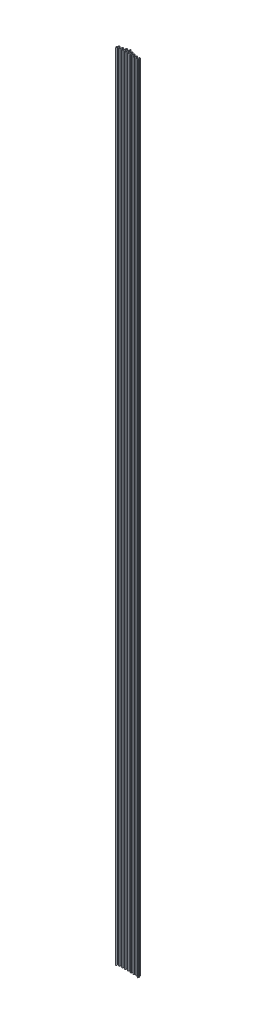
SolidWorks part; units mm, degrees
material "6463-T6"
ref_plane "Front Plane" through (0, 0, 0) normal (0, 0, 1) x (1, 0, 0)
ref_plane "Top Plane" through (0, 0, 0) normal (0, 1, 0) x (1, 0, 0)
ref_plane "Right Plane" through (0, 0, 0) normal (1, 0, 0) x (0, 0, -1)
sketch "Sketch1" plane through (0, 0, 0) normal (0, 1, 0) x (1, 0, 0)
  line L0 (0, 0) -> (101.6, 0) construction
  line L1 (0, 0) -> (0, 19.05) construction
  line L2 (0, 19.05) -> (101.6, 19.05) construction
  line L3 (101.6, 19.05) -> (101.6, 0) construction
  line L4 (0, 6.35) -> (101.6, 6.35) construction
  line L5 (0, 8.89) -> (101.6, 8.89) construction
  line L6 (0, 12.7) -> (101.6, 12.7) construction
  line L7 (0, 16.51) -> (101.6, 16.51) construction
  line L8 (6.35, 0) -> (6.35, 19.05) construction
  line L9 (12.7, 0) -> (12.7, 19.05) construction
  line L10 (19.05, 0) -> (19.05, 19.05) construction
  line L11 (25.4, 0) -> (25.4, 19.05) construction
  line L12 (31.75, 0) -> (31.75, 19.05) construction
  line L13 (38.1, 0) -> (38.1, 19.05) construction
  line L14 (44.45, 0) -> (44.45, 19.05) construction
  line L15 (50.8, 0) -> (50.8, 19.05) construction
  line L16 (57.15, 0) -> (57.15, 19.05) construction
  line L17 (63.5, 0) -> (63.5, 19.05) construction
  line L18 (69.85, 0) -> (69.85, 19.05) construction
  line L19 (76.2, 0) -> (76.2, 19.05) construction
  line L20 (82.55, 0) -> (82.55, 19.05) construction
  line L21 (88.9, 0) -> (88.9, 19.05) construction
  line L22 (95.25, 0) -> (95.25, 19.05) construction
  line L23 (0, 1.6002) -> (101.6, 1.6002) construction
  line L24 (0, 3.2004) -> (101.6, 3.2004) construction
  line L25 (1.4865, 1.0077) -> (3.9905, 7.2904)
  line L26 (11.2135, 1.0077) -> (8.7095, 7.2904)
  line L27 (16.6048, 9.5774) -> (14.2405, 1.1671)
  line L28 (23.8595, 1.1671) -> (21.4952, 9.5774)
  line L29 (26.9714, 1.2981) -> (29.2557, 13.1795)
  line L30 (36.5286, 1.2981) -> (34.2443, 13.1795)
  line L31 (39.6836, 1.3701) -> (41.9364, 16.8752)
  line L32 (49.2164, 1.3701) -> (46.9636, 16.8752)
  line L33 (52.3714, 1.2981) -> (54.6557, 13.1795)
  line L34 (61.9286, 1.2981) -> (59.6443, 13.1795)
  line L35 (65.0405, 1.1671) -> (67.4048, 9.5774)
  line L36 (74.6595, 1.1671) -> (72.2952, 9.5774)
  line L37 (77.6865, 1.0077) -> (80.1905, 7.2904)
  line L38 (87.4135, 1.0077) -> (84.9095, 7.2904)
  line L39 (90.3865, 1.0077) -> (92.8905, 7.2904)
  line L40 (100.1135, 1.0077) -> (97.6095, 7.2904)
  line L59 (2.9022, 0.4435) -> (5.4062, 6.7262)
  line L60 (9.7978, 0.4435) -> (7.2938, 6.7262)
  line L61 (18.0719, 9.165) -> (15.7076, 0.7547)
  line L62 (22.3924, 0.7547) -> (20.0281, 9.165)
  line L63 (28.468, 1.0104) -> (30.7523, 12.8918)
  line L64 (35.032, 1.0104) -> (32.7477, 12.8918)
  line L65 (41.1917, 1.151) -> (43.4446, 16.6561)
  line L66 (47.7083, 1.151) -> (45.4554, 16.6561)
  line L67 (53.868, 1.0104) -> (56.1523, 12.8918)
  line L68 (60.432, 1.0104) -> (58.1477, 12.8918)
  line L69 (66.5076, 0.7547) -> (68.8719, 9.165)
  line L70 (73.1924, 0.7547) -> (70.8281, 9.165)
  line L71 (79.1022, 0.4435) -> (81.6062, 6.7262)
  line L72 (85.9978, 0.4435) -> (83.4938, 6.7262)
  line L73 (91.8022, 0.4435) -> (94.3062, 6.7262)
  line L74 (98.6978, 0.4435) -> (96.1938, 6.7262)
  line L75 (101.6, 0) -> (101.6, -1.524)
  line L76 (0, 0) -> (0, -1.524)
  arc A1 (8.7095, 7.2904) -> (3.9905, 7.2904) centre (6.35, 6.35) ccw
  arc A2 (21.4952, 9.5774) -> (16.6048, 9.5774) centre (19.05, 8.89) ccw
  arc A3 (34.2443, 13.1795) -> (29.2557, 13.1795) centre (31.75, 12.7) ccw
  arc A6 (72.2952, 9.5774) -> (67.4048, 9.5774) centre (69.85, 8.89) ccw
  arc A7 (84.9095, 7.2904) -> (80.1905, 7.2904) centre (82.55, 6.35) ccw
  arc A8 (97.6095, 7.2904) -> (92.8905, 7.2904) centre (95.25, 6.35) ccw
  arc A9 (0, 0) -> (1.4865, 1.0077) centre (0, 1.6002) ccw
  arc A10 (11.2135, 1.0077) -> (14.2405, 1.1671) centre (12.7, 1.6002) ccw
  arc A11 (23.8595, 1.1671) -> (26.9714, 1.2981) centre (25.4, 1.6002) ccw
  arc A12 (36.5286, 1.2981) -> (39.6836, 1.3701) centre (38.1, 1.6002) ccw
  arc A13 (49.2164, 1.3701) -> (52.3714, 1.2981) centre (50.8, 1.6002) ccw
  arc A14 (61.9286, 1.2981) -> (65.0405, 1.1671) centre (63.5, 1.6002) ccw
  arc A15 (74.6595, 1.1671) -> (77.6865, 1.0077) centre (76.2, 1.6002) ccw
  arc A16 (87.4135, 1.0077) -> (90.3865, 1.0077) centre (88.9, 1.6002) ccw
  arc A17 (100.1135, 1.0077) -> (101.6, 0) centre (101.6, 1.6002) ccw
  arc A35 (59.6443, 13.1795) -> (54.6557, 13.1795) centre (57.15, 12.7) ccw
  arc A36 (0, -1.524) -> (2.9022, 0.4435) centre (0, 1.6002) ccw
  arc A37 (7.2938, 6.7262) -> (5.4062, 6.7262) centre (6.35, 6.35) ccw
  arc A38 (9.7978, 0.4435) -> (15.7076, 0.7547) centre (12.7, 1.6002) ccw
  arc A39 (46.9636, 16.8752) -> (41.9364, 16.8752) centre (44.45, 16.51) ccw
  arc A40 (20.0281, 9.165) -> (18.0719, 9.165) centre (19.05, 8.89) ccw
  arc A41 (22.3924, 0.7547) -> (28.468, 1.0104) centre (25.4, 1.6002) ccw
  arc A42 (32.7477, 12.8918) -> (30.7523, 12.8918) centre (31.75, 12.7) ccw
  arc A43 (35.032, 1.0104) -> (41.1917, 1.151) centre (38.1, 1.6002) ccw
  arc A44 (45.4554, 16.6561) -> (43.4446, 16.6561) centre (44.45, 16.51) ccw
  arc A45 (47.7083, 1.151) -> (53.868, 1.0104) centre (50.8, 1.6002) ccw
  arc A46 (58.1477, 12.8918) -> (56.1523, 12.8918) centre (57.15, 12.7) ccw
  arc A47 (60.432, 1.0104) -> (66.5076, 0.7547) centre (63.5, 1.6002) ccw
  arc A48 (70.8281, 9.165) -> (68.8719, 9.165) centre (69.85, 8.89) ccw
  arc A49 (73.1924, 0.7547) -> (79.1022, 0.4435) centre (76.2, 1.6002) ccw
  arc A50 (83.4938, 6.7262) -> (81.6062, 6.7262) centre (82.55, 6.35) ccw
  arc A51 (85.9978, 0.4435) -> (91.8022, 0.4435) centre (88.9, 1.6002) ccw
  arc A52 (96.1938, 6.7262) -> (94.3062, 6.7262) centre (95.25, 6.35) ccw
  arc A53 (98.6978, 0.4435) -> (101.6, -1.524) centre (101.6, 1.6002) ccw
other "AlignGroup1"
other "AlignGroup2"
other "AlignGroup3" parameters "D10"=2.4117, "D13"=3.2004, "D14"=6.511, "D1"=86.8219, "D2"=13.2255, "D3"=6.35, "D4"=8.89, "D5"=12.7, "D6"=16.51, "D7"=19.05, "D8"=19.05, "D9"=5.2861, "D11"=101.6, "D12"=101.6
extrude "Boss-Extrude1" add sketch "Sketch1" against normal blind 3505.2
sketch "Sketch3" plane through (0, 0, 0) normal (0, 1, 0) x (1, 0, 0)
  line L0 (0, -0.762) -> (0, -1.524)
  line L1 (0, 0) -> (0, -1.524) construction
  line L2 (0, -1.524) -> (0.2773, -1.524)
  line L3 (0.2773, -1.524) -> (0, -0.762)
  line L4 (101.6, -0.762) -> (101.6, -1.524)
  line L5 (101.6, -1.524) -> (101.6, 0) construction
  line L6 (101.6, -1.524) -> (101.3227, -1.524)
  line L7 (101.3227, -1.524) -> (101.6, -0.762)
  dimension "D1" = 0.762
  dimension "D2" = 20
  dimension "D3" = 0.762
  dimension "D4" = 20
extrude "Cut-Extrude1" cut sketch "Sketch3" against normal through all
sketch "Sketch4" plane through (0, 0, 0) normal (0, 1, 0) x (1, 0, 0)
  line L0 (2.9022, 0.4435) -> (5.4062, 6.7262) construction
  line L1 (0.273, -1.512) -> (0, -0.762) construction
  line L2 (2.9022, 0.4435) -> (3.0155, 0.7277)
  line L3 (1.6375, -5.261) -> (1.411, -4.6388)
  line L4 (2.794, -1.7145) -> (0.3467, -1.7145)
  line L5 (2.794, -4.1275) -> (1.7691, -4.1275)
  line L6 (0.3467, -1.7145) -> (0.273, -1.512)
  line L7 (50.8, 25.7649) -> (50.8, -11.8096) construction
  line L8 (101.2533, -1.7145) -> (101.327, -1.512)
  line L9 (98.806, -4.1275) -> (99.8309, -4.1275)
  line L10 (98.806, -1.7145) -> (101.2533, -1.7145)
  line L11 (99.9625, -5.261) -> (100.189, -4.6388)
  line L12 (98.6978, 0.4435) -> (98.5845, 0.7277)
  arc A0 (0.273, -1.512) -> (2.9022, 0.4435) centre (0, 1.6002) ccw construction
  arc A1 (0.273, -1.512) -> (2.9022, 0.4435) centre (0, 1.6002) ccw
  arc A2 (2.794, -4.1275) -> (2.794, -1.7145) centre (2.794, -2.921) ccw
  arc A3 (1.866, -5.489) -> (3.5206, -0.2889) centre (2.794, -2.921) ccw
  arc A4 (1.6375, -5.261) -> (1.866, -5.489) centre (1.9955, -5.1307) ccw
  arc A5 (1.7691, -4.1275) -> (1.411, -4.6388) centre (1.7691, -4.5085) ccw
  arc A6 (3.0155, 0.7277) -> (3.5206, -0.2889) centre (3.7233, 0.4456) ccw
  arc A7 (98.5845, 0.7277) -> (98.0794, -0.2889) centre (97.8767, 0.4456) cw
  arc A8 (99.8309, -4.1275) -> (100.189, -4.6388) centre (99.8309, -4.5085) cw
  arc A9 (99.9625, -5.261) -> (99.734, -5.489) centre (99.6045, -5.1307) cw
  arc A10 (99.734, -5.489) -> (98.0794, -0.2889) centre (98.806, -2.921) cw
  arc A11 (98.806, -4.1275) -> (98.806, -1.7145) centre (98.806, -2.921) cw
  arc A12 (101.327, -1.512) -> (98.6978, 0.4435) centre (101.6, 1.6002) cw
  dimension "D1" = 2.413
  dimension "D2" = 5.461
  dimension "D5" = 0.381
  dimension "D6" = 0.762
  dimension "D3" = 2.794
  dimension "D4" = 2.921
  dimension "D7" = 50.8
extrude "Boss-Extrude2" add sketch "Sketch4" against normal through all
fillet "Fillet1" radius 0.508 2 edges at (101.2533, -1752.6, 1.7145) (0.3467, -1752.6, 1.7145)
